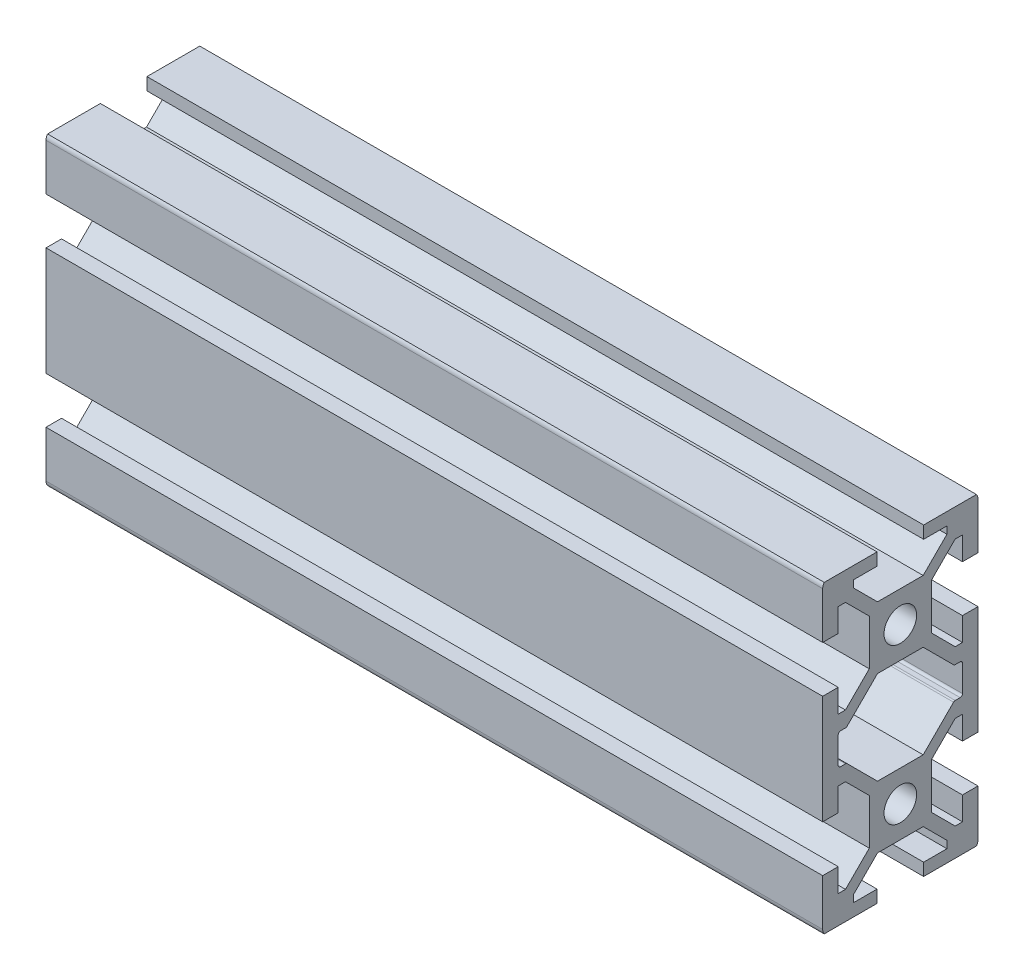
SolidWorks part; units mm, degrees
ref_plane "Front Plane" through (0, 0, 0) normal (0, 0, 1) x (1, 0, 0)
ref_plane "Top Plane" through (0, 0, 0) normal (0, 1, 0) x (1, 0, 0)
ref_plane "Right Plane" through (0, 0, 0) normal (1, 0, 0) x (0, 0, -1)
sketch "Sketch1" plane through (0, 0, 0) normal (1, 0, 0) x (0, 0, -1)
  line L1 (-8, 1.7) -> (-8, -1.7)
  line L2 (-7.0636, 2) -> (-7.7, 2)
  line L3 (-2.9393, 6) -> (-6.8515, 2.0879)
  line L4 (2.9393, 6) -> (-2.9393, 6)
  line L5 (6.8515, 2.0879) -> (2.9393, 6)
  line L6 (7.7, 2) -> (7.0636, 2)
  line L7 (8, -1.7) -> (8, 1.7)
  line L8 (7.0636, -2) -> (7.7, -2)
  line L9 (2.9393, -6) -> (6.8515, -2.0879)
  line L10 (-2.9393, -6) -> (2.9393, -6)
  line L11 (-6.8515, -2.0879) -> (-2.9393, -6)
  line L12 (-7.7, -2) -> (-7.0636, -2)
  line L13 (-10, 7) -> (-10, -7)
  line L14 (-10, -7) -> (-8, -7)
  line L15 (-8, -7) -> (-8, -4)
  line L16 (-8, -4) -> (-7.0607, -4)
  line L17 (-7.0607, -4) -> (-4, -7.0607)
  line L18 (-4, -7.0607) -> (-4, -12.9393)
  line L22 (-4, -12.9393) -> (-7.0607, -16)
  line L23 (-7.0607, -16) -> (-8, -16)
  line L24 (-8, -16) -> (-8, -13)
  line L25 (-8, -13) -> (-10, -13)
  line L26 (-10, -13) -> (-10, -19)
  line L27 (-9.8, -19.6) -> (-3, -19.6)
  line L28 (-3, -19.6) -> (-3, -18)
  line L29 (-3, -18) -> (-6, -18)
  line L30 (-6, -18) -> (-6, -17.0607)
  line L31 (-6, -17.0607) -> (-2.9393, -14)
  line L32 (-2.9393, -14) -> (2.9393, -14)
  line L36 (2.9393, -14) -> (6, -17.0607)
  line L37 (6, -17.0607) -> (6, -18)
  line L38 (6, -18) -> (3, -18)
  line L39 (3, -18) -> (3, -19.6)
  line L40 (3, -19.6) -> (9.8, -19.6)
  line L41 (10, -19) -> (10, -13)
  line L42 (10, -13) -> (8, -13)
  line L43 (8, -13) -> (8, -16)
  line L44 (8, -16) -> (7.0607, -16)
  line L45 (7.0607, -16) -> (4, -12.9393)
  line L49 (4, -12.9393) -> (4, -7.0607)
  line L50 (4, -7.0607) -> (7.0607, -4)
  line L51 (7.0607, -4) -> (8, -4)
  line L52 (8, -4) -> (8, -7)
  line L53 (8, -7) -> (10, -7)
  line L54 (10, -7) -> (10, 7)
  line L55 (10, 7) -> (8, 7)
  line L56 (8, 7) -> (8, 4)
  line L57 (8, 4) -> (7.0607, 4)
  line L58 (7.0607, 4) -> (4, 7.0607)
  line L62 (4, 7.0607) -> (4, 12.9393)
  line L63 (4, 12.9393) -> (7.0607, 16)
  line L64 (7.0607, 16) -> (8, 16)
  line L65 (8, 16) -> (8, 13)
  line L66 (8, 13) -> (10, 13)
  line L67 (10, 13) -> (10, 19)
  line L68 (9.8, 19.6) -> (3, 19.6)
  line L69 (3, 19.6) -> (3, 18)
  line L70 (3, 18) -> (6, 18)
  line L71 (6, 18) -> (6, 17.0607)
  line L72 (6, 17.0607) -> (2.9393, 14)
  line L76 (2.9393, 14) -> (-2.9393, 14)
  line L77 (-2.9393, 14) -> (-6, 17.0607)
  line L78 (-6, 17.0607) -> (-6, 18)
  line L79 (-6, 18) -> (-3, 18)
  line L80 (-3, 18) -> (-3, 19.6)
  line L81 (-3, 19.6) -> (-9.8, 19.6)
  line L82 (-10, 19) -> (-10, 13)
  line L83 (-10, 13) -> (-8, 13)
  line L84 (-8, 13) -> (-8, 16)
  line L85 (-8, 16) -> (-7.0607, 16)
  line L86 (-7.0607, 16) -> (-4, 12.9393)
  line L87 (-4, 12.9393) -> (-4, 7.0607)
  line L91 (-4, 7.0607) -> (-7.0607, 4)
  line L92 (-7.0607, 4) -> (-8, 4)
  line L93 (-8, 4) -> (-8, 7)
  line L94 (-8, 7) -> (-10, 7)
  circle A0 centre (0, 10) radius 2.1
  arc A1 (-10, -19) -> (-9.8, -19.6) centre (-9, -19) ccw
  arc A2 (9.8, -19.6) -> (10, -19) centre (9, -19) ccw
  arc A3 (10, 19) -> (9.8, 19.6) centre (9, 19) ccw
  arc A4 (-9.8, 19.6) -> (-10, 19) centre (-9, 19) ccw
  circle A5 centre (0, -10) radius 2.1
  arc A6 (-7.7, 2) -> (-8, 1.7) centre (-7.7, 1.7) ccw
  arc A7 (-7.0636, 2) -> (-6.8515, 2.0879) centre (-7.0636, 2.3) ccw
  arc A8 (6.8515, 2.0879) -> (7.0636, 2) centre (7.0636, 2.3) ccw
  arc A9 (8, 1.7) -> (7.7, 2) centre (7.7, 1.7) ccw
  arc A10 (7.7, -2) -> (8, -1.7) centre (7.7, -1.7) ccw
  arc A11 (7.0636, -2) -> (6.8515, -2.0879) centre (7.0636, -2.3) ccw
  arc A12 (-6.8515, -2.0879) -> (-7.0636, -2) centre (-7.0636, -2.3) ccw
  arc A13 (-8, -1.7) -> (-7.7, -2) centre (-7.7, -1.7) ccw
  dimension "A" = 20
  dimension "T" = 39.2
extrude "Boss-Extrude1" add sketch "Sketch1" along normal blind 100
ref_plane "Plane1" through (0, 19.6, 0) normal (0, 1, 0) x (1, 0, 0)
ref_plane "Plane2" through (0, 0, 0) normal (1, 0, 0) x (0, 0, -1)
ref_plane "Plane3" through (100, 0, 0) normal (1, 0, 0) x (0, 0, -1)
sketch "Sketch2" [suppressed] plane through (0, 0, 0) normal (0, 0, 1) x (1, 0, 0)
  line L0 (7, -19.6) -> (9.75, -19.6)
  line L1 (9.75, -19.6) -> (9.75, 14)
  line L2 (9.75, 14) -> (11.75, 14)
  line L3 (11.75, 14) -> (11.75, 19.6)
  line L4 (11.75, 19.6) -> (7, 19.6)
  line L5 (7, 19.6) -> (7, -19.6) construction
  line L6 (7, 19.6) -> (7, -19.6)
  point P7 (7, 0)
  dimension "T" = 39.2
  dimension "D1_s" = 9.5
  dimension "D_s" = 5.5
  dimension "FIX_3" = 5.6
  dimension "XA" = 7
revolve "Cut-Revolve1" [suppressed] cut sketch "Sketch2" angle 360 about L5
sketch "Sketch3" [suppressed] plane through (0, 0, 0) normal (0, 0, 1) x (1, 0, 0)
  line L0 (18.5, 19.6) -> (18.5, -19.6) construction
  line L1 (18.5, -19.6) -> (21.25, -19.6)
  line L2 (21.25, -19.6) -> (21.25, 14)
  line L3 (21.25, 14) -> (23.25, 14)
  line L4 (23.25, 14) -> (23.25, 19.6)
  line L5 (23.25, 19.6) -> (18.5, 19.6)
  line L7 (18.5, 19.6) -> (18.5, -19.6)
  point P6 (18.5, 0)
  dimension "D1_s" = 9.5
  dimension "D_s" = 5.5
  dimension "T" = 39.2
  dimension "FIX_5" = 5.6
  dimension "XB" = 19
revolve "Cut-Revolve2" [suppressed] cut sketch "Sketch3" angle 360 about L0
sketch "Sketch4" [suppressed] plane through (0, 0, 0) normal (0, 0, 1) x (1, 0, 0)
  line L0 (30, 19.6) -> (30, -19.6) construction
  line L1 (30, -19.6) -> (32.75, -19.6)
  line L2 (32.75, -19.6) -> (32.75, 14)
  line L3 (32.75, 14) -> (34.75, 14)
  line L4 (34.75, 14) -> (34.75, 19.6)
  line L5 (34.75, 19.6) -> (30, 19.6)
  line L6 (30, 19.6) -> (30, -19.6)
  point P2 (30, 0)
  dimension "D1_s" = 9.5
  dimension "D_s" = 5.5
  dimension "T" = 39.2
  dimension "FIX_7" = 5.6
  dimension "XC" = 31
revolve "Cut-Revolve3" [suppressed] cut sketch "Sketch4" angle 360 about L0
sketch "Sketch5" [suppressed] plane through (0, 0, 0) normal (0, 0, 1) x (1, 0, 0)
  line L0 (41.5, 19.6) -> (41.5, -19.6) construction
  line L1 (41.5, -19.6) -> (44.25, -19.6)
  line L2 (44.25, -19.6) -> (44.25, 14)
  line L3 (44.25, 14) -> (46.25, 14)
  line L4 (46.25, 14) -> (46.25, 19.6)
  line L5 (46.25, 19.6) -> (41.5, 19.6)
  line L7 (41.5, 19.6) -> (41.5, -19.6)
  point P6 (41.5, 0)
  dimension "D1_s" = 9.5
  dimension "D_s" = 5.5
  dimension "FIX_9" = 5.6
  dimension "T" = 39.2
  dimension "XD" = 43
revolve "Cut-Revolve4" [suppressed] cut sketch "Sketch5" angle 360 about L0
sketch "Sketch6" [suppressed] plane through (0, 0, 0) normal (0, 0, 1) x (1, 0, 0)
  line L0 (53, 19.6) -> (53, -19.6) construction
  line L1 (53, -19.6) -> (55.75, -19.6)
  line L2 (55.75, -19.6) -> (55.75, 14)
  line L3 (55.75, 14) -> (57.75, 14)
  line L4 (57.75, 14) -> (57.75, 19.6)
  line L5 (57.75, 19.6) -> (53, 19.6)
  line L6 (53, 19.6) -> (53, -19.6)
  point P6 (53, 0)
  dimension "XE" = 55
  dimension "D1_s" = 9.5
  dimension "D_s" = 5.5
  dimension "T" = 39.2
  dimension "FIX_11" = 5.6
revolve "Cut-Revolve5" [suppressed] cut sketch "Sketch6" angle 360 about L0
sketch "Sketch7" [suppressed] plane through (0, 19.6, 0) normal (0, 1, 0) x (1, 0, 0)
  circle A0 centre (7, 0) radius 3.675
  dimension "D" = 7.35
  dimension "AV" = 7
extrude "Cut-Extrude1" [suppressed] cut sketch "Sketch7" against normal blind 39.2
sketch "Sketch8" [suppressed] plane through (0, 19.6, 0) normal (0, 1, 0) x (1, 0, 0)
  circle A0 centre (18.5, 0) radius 3.675
  dimension "D" = 7.35
  dimension "BV" = 19
extrude "Cut-Extrude2" [suppressed] cut sketch "Sketch8" against normal blind 39.2
sketch "Sketch9" [suppressed] plane through (0, 19.6, 0) normal (0, 1, 0) x (1, 0, 0)
  circle A0 centre (30, 0) radius 3.675
  dimension "D" = 7.35
  dimension "CV" = 31
extrude "Cut-Extrude3" [suppressed] cut sketch "Sketch9" against normal blind 39.2
sketch "Sketch10" [suppressed] plane through (0, 19.6, 0) normal (0, 1, 0) x (1, 0, 0)
  circle A0 centre (41.5, 0) radius 3.675
  dimension "D" = 7.35
  dimension "DV" = 43
extrude "Cut-Extrude4" [suppressed] cut sketch "Sketch10" against normal blind 39.2
sketch "Sketch11" [suppressed] plane through (0, 19.6, 0) normal (0, 1, 0) x (1, 0, 0)
  circle A0 centre (53, 0) radius 3.675
  dimension "D" = 7.35
  dimension "EV" = 55
extrude "Cut-Extrude5" [suppressed] cut sketch "Sketch11" against normal blind 39.2
sketch "Sketch12" [suppressed] plane through (0, 0, 0) normal (1, 0, 0) x (0, 0, -1)
  circle A0 centre (0, -10) radius 2.1
  circle A1 centre (0, 10) radius 2.1
  dimension "FIX_13" = 4.2
  dimension "FIX_14" = 10
  dimension "FIX_15" = 20
extrude "Boss-Extrude2" [suppressed] add sketch "Sketch12" along normal blind 15
hole_wizard "Tapped Hole1" [suppressed] positions "Sketch14" profile "Sketch13" tap size "M5x0.8" standard "JIS"
sketch "Sketch14" [suppressed] plane through (0, 0, 0) normal (1, 0, 0) x (0, 0, -1)
  point P0 (0, -10)
  point P9 (0, 10)
  dimension "FIX_17" = 20
  dimension "FIX_18" = 10
sketch "Sketch13" [suppressed] plane through (0, -10, 0) normal (0, 1, 0) x (0, 0, 1)
  line L0 (0, 0) -> (0, 15)
  line L1 (0, 15) -> (2.1, 15)
  line L2 (2.1, 15) -> (2.1, 0)
  line L5 (2.1, 0) -> (0, 0)
  line L11 (0, -6.35) -> (0, 107.95) construction
  dimension "Thru Tap Drill Dia." = 4.2
  dimension "Thru Tap Drill Depth" = 15
cosmetic thread "Hole Thread1" [suppressed] parameters "NFIX_2"=15, "NFIX_1"=5
cosmetic thread "Hole Thread2" [suppressed] parameters "NFIX_2"=15, "NFIX_1"=5
sketch "Sketch15" [suppressed] plane through (100, 0, 0) normal (1, 0, 0) x (0, 0, -1)
  circle A0 centre (0, -10) radius 2.1
  circle A1 centre (0, 10) radius 2.1
  dimension "FIX_19" = 4.2
  dimension "FIX_20" = 20
  dimension "FIX_21" = 10
extrude "Boss-Extrude3" [suppressed] add sketch "Sketch15" against normal blind 15
hole_wizard "Tapped Hole2" [suppressed] positions "Sketch17" profile "Sketch16" tap size "M5x0.8" standard "JIS"
sketch "Sketch17" [suppressed] plane through (100, 0, 0) normal (1, 0, 0) x (0, 0, -1)
  point P0 (0, -10)
  point P8 (0, 10)
  dimension "FIX_23" = 10
  dimension "FIX_24" = 20
sketch "Sketch16" [suppressed] plane through (100, -10, 0) normal (0, 1, 0) x (0, 0, -1)
  line L0 (0, 0) -> (0, 15)
  line L1 (0, 15) -> (2.1, 15)
  line L2 (2.1, 15) -> (2.1, 0)
  line L5 (2.1, 0) -> (0, 0)
  line L11 (0, -6.35) -> (0, 107.95) construction
  dimension "Thru Tap Drill Dia." = 4.2
  dimension "Thru Tap Drill Depth" = 15
cosmetic thread "Hole Thread3" [suppressed] parameters "NFIX_2"=15, "NFIX_1"=5
cosmetic thread "Hole Thread4" [suppressed] parameters "NFIX_2"=15, "NFIX_1"=5
sketch "Sketch18" [suppressed] plane through (0, 0, 0) normal (1, 0, 0) x (0, 0, -1)
  circle A0 centre (0, -10) radius 2.1
  circle A1 centre (0, 10) radius 2.1
  dimension "FIX_25" = 4.2
  dimension "FIX_26" = 20
  dimension "FIX_27" = 10
extrude "Boss-Extrude4" [suppressed] add sketch "Sketch18" along normal blind 15
sketch "Sketch19" [suppressed] plane through (100, 0, 0) normal (1, 0, 0) x (0, 0, -1)
  circle A0 centre (0, -10) radius 2.1
  circle A1 centre (0, 10) radius 2.1
  dimension "FIX_29" = 4.2
  dimension "FIX_30" = 20
  dimension "FIX_31" = 10
extrude "Boss-Extrude5" [suppressed] add sketch "Sketch19" against normal blind 15
hole_wizard "Tapped Hole3" [suppressed] positions "Sketch21" profile "Sketch20" tap size "M5x0.8" standard "JIS"
sketch "Sketch21" [suppressed] plane through (0, 0, 0) normal (1, 0, 0) x (0, 0, -1)
  point P5 (0, 10)
  point P7 (0, -10)
  dimension "FIX_33" = 20
  dimension "FIX_34" = 10
sketch "Sketch20" [suppressed] plane through (0, 10, 0) normal (0, 1, 0) x (0, 0, 1)
  line L0 (0, 0) -> (0, 15)
  line L1 (0, 15) -> (2.1, 15)
  line L2 (2.1, 15) -> (2.1, 0)
  line L5 (2.1, 0) -> (0, 0)
  line L11 (0, -6.35) -> (0, 107.95) construction
  dimension "Thru Tap Drill Dia." = 4.2
  dimension "Thru Tap Drill Depth" = 15
cosmetic thread "Hole Thread5" [suppressed] parameters "NFIX_2"=15, "NFIX_1"=5
cosmetic thread "Hole Thread6" [suppressed] parameters "NFIX_2"=15, "NFIX_1"=5
hole_wizard "Tapped Hole4" [suppressed] positions "Sketch23" profile "Sketch22" tap size "M5x0.8" standard "JIS"
sketch "Sketch23" [suppressed] plane through (100, 0, 0) normal (1, 0, 0) x (0, 0, -1)
  point P5 (0, 10)
  point P7 (0, -10)
  dimension "FIX_35" = 20
  dimension "FIX_36" = 10
sketch "Sketch22" [suppressed] plane through (100, 10, 0) normal (0, 1, 0) x (0, 0, -1)
  line L0 (0, 0) -> (0, 15)
  line L1 (0, 15) -> (2.1, 15)
  line L2 (2.1, 15) -> (2.1, 0)
  line L5 (2.1, 0) -> (0, 0)
  line L11 (0, -6.35) -> (0, 107.95) construction
  dimension "Thru Tap Drill Dia." = 4.2
  dimension "Thru Tap Drill Depth" = 15
cosmetic thread "Hole Thread7" [suppressed] parameters "NFIX_2"=15, "NFIX_1"=5
cosmetic thread "Hole Thread8" [suppressed] parameters "NFIX_2"=15, "NFIX_1"=5
